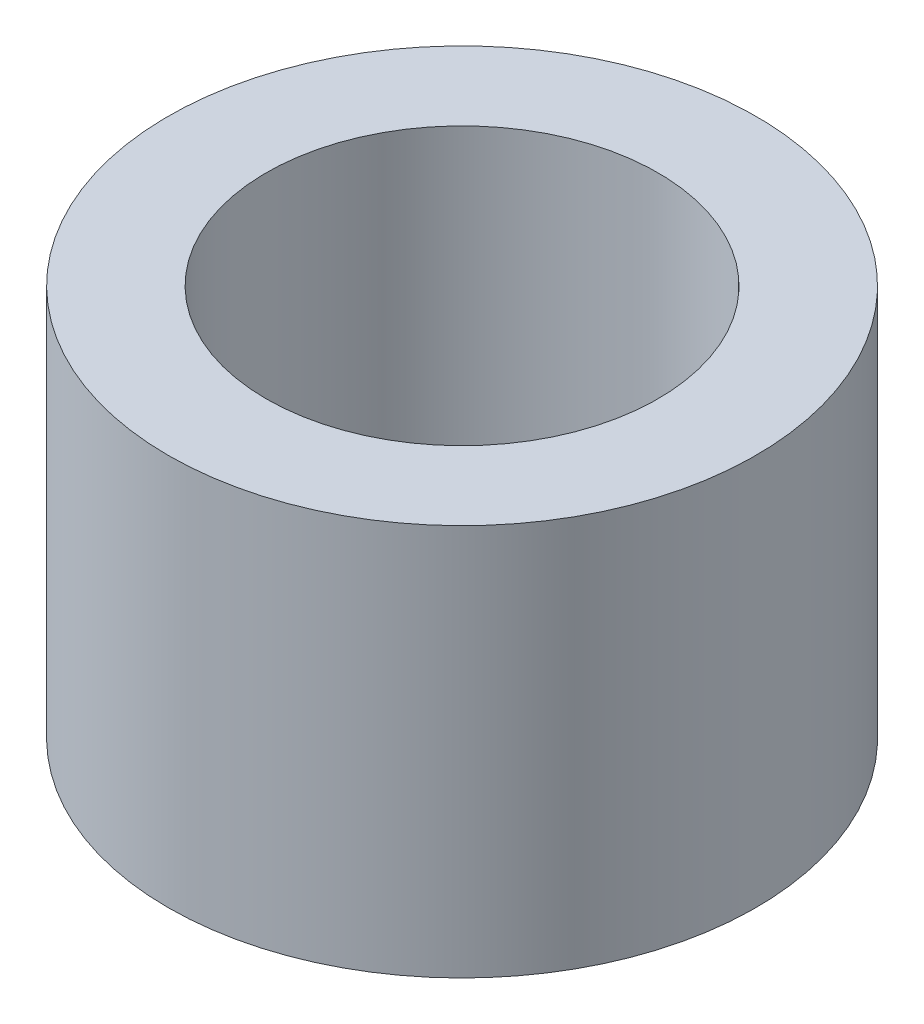
SolidWorks part; units mm, degrees
material "Brass"
ref_plane "Front Plane" through (0, 0, 0) normal (0, 0, 1) x (1, 0, 0)
ref_plane "Top Plane" through (0, 0, 0) normal (0, 1, 0) x (1, 0, 0)
ref_plane "Right Plane" through (0, 0, 0) normal (1, 0, 0) x (0, 0, -1)
sketch "Sketch1" plane through (0, 0, 0) normal (0, 0, 1) x (1, 0, 0)
  line L0 (0, 3.175) -> (0, -3.175) construction
  line L1 (-4.7625, -3.175) -> (-3.175, -3.175)
  line L2 (-4.7625, -3.175) -> (-4.7625, 3.175)
  line L3 (-4.7625, 3.175) -> (-3.175, 3.175)
  line L4 (-3.175, -3.175) -> (-3.175, 3.175)
  line L5 (-4.7625, -3.175) -> (-3.175, 3.175) construction
  line L6 (-4.7625, 3.175) -> (-3.175, -3.175) construction
  point P0 (-3.9687, 0)
  point P5 (0, 0)
  point P9 (0, 0)
  point P11 (0, 0)
  dimension "D1" = 4.7625
  dimension "D2" = 3.175
  dimension "D3" = 6.35
revolve "Revolve1" add sketch "Sketch1" angle 360 about L0
